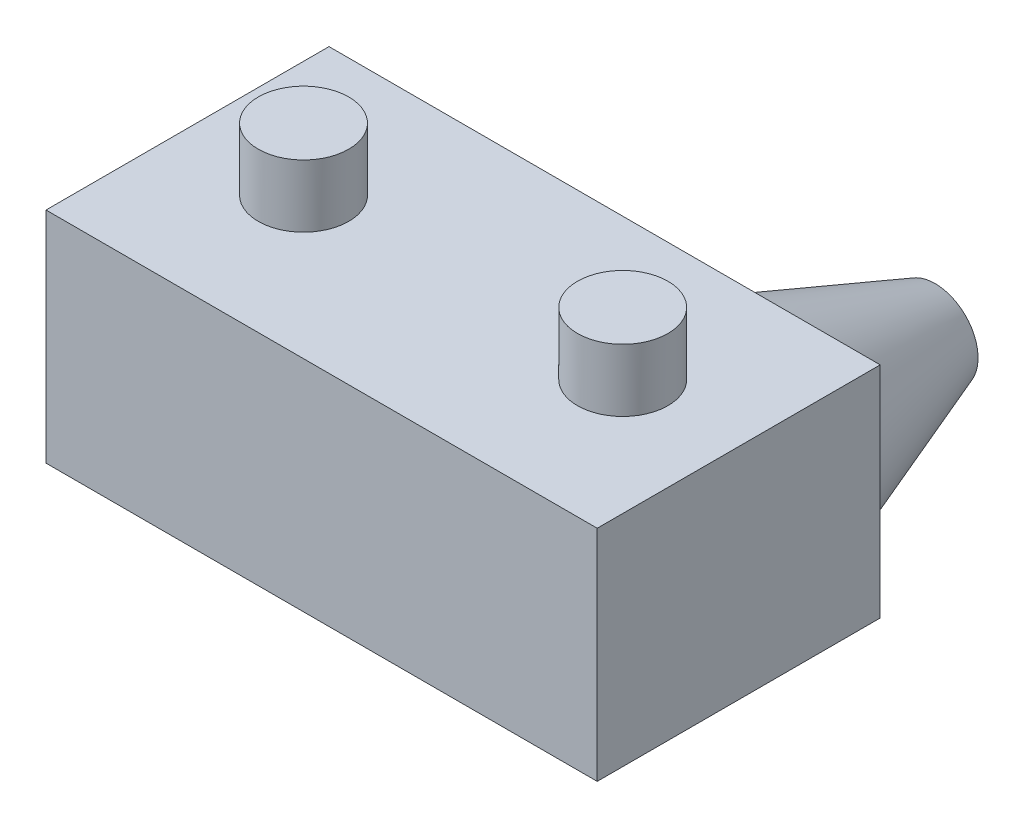
SolidWorks part; units mm, degrees
ref_plane "Front Plane" through (0, 0, 0) normal (0, 0, 1) x (1, 0, 0)
ref_plane "Top Plane" through (0, 0, 0) normal (0, 1, 0) x (1, 0, 0)
ref_plane "Right Plane" through (0, 0, 0) normal (1, 0, 0) x (0, 0, -1)
sketch "Sketch1" plane through (0, 0, 0) normal (0, 0, 1) x (1, 0, 0)
  line L1 (-13.4, 5.33) -> (0, 5.33)
  line L2 (-13.4, 5.33) -> (-13.4, 0)
  line L3 (-13.4, 0) -> (0, 0)
  line L4 (0, 5.33) -> (0, 0)
  point P4 (0, 0)
  dimension "D1" = 13.4
  dimension "D2" = 5.33
extrude "Boss-Extrude1" add sketch "Sketch1" along normal blind 6.88
sketch "Sketch2" plane through (0, 5.33, 0) normal (0, 1, 0) x (1, 0, 0)
  line L0 (-13.4, -3.44) -> (-11.68, -3.44) construction
  line L1 (-13.4, -6.88) -> (-13.4, 0) construction
  line L2 (0, -6.88) -> (0, 0) construction
  line L3 (-1.72, -3.44) -> (0, -3.44) construction
  line L4 (-9.48, -3.44) -> (-3.92, -3.44) construction
  circle A0 centre (-10.58, -3.44) radius 1.1
  circle A1 centre (-2.82, -3.44) radius 1.1
  dimension "D1" = 2.2
  dimension "D2" = 5.56
extrude "Boss-Extrude2" add sketch "Sketch2" along normal blind 1.52
sketch "Sketch3" plane through (0, 0, 0) normal (0, 0, -1) x (-1, 0, 0)
  line L0 (2.665, 2.665) -> (0, 2.665) construction
  line L1 (0, 0) -> (0, 5.33) construction
  line L2 (2.665, 2.665) -> (2.665, 5.33) construction
  line L3 (0, 5.33) -> (13.4, 5.33) construction
  line L4 (2.665, 2.665) -> (2.665, 0) construction
  line L5 (13.4, 0) -> (0, 0) construction
  circle A0 centre (2.665, 2.665) radius 2.5
  dimension "D1" = 5
extrude "Boss-Extrude3" add sketch "Sketch3" along normal blind 4 draft 20
